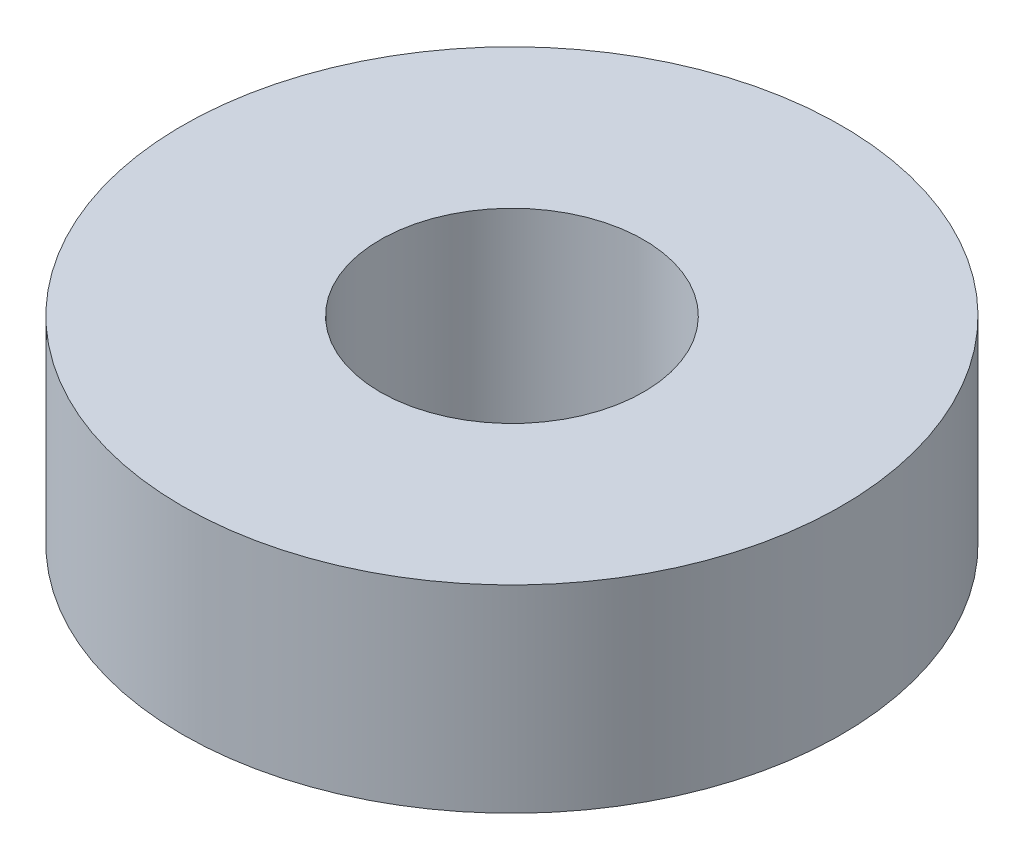
SolidWorks part; units mm, degrees
ref_plane "Front Plane" through (0, 0, 0) normal (0, 0, 1) x (1, 0, 0)
ref_plane "Top Plane" through (0, 0, 0) normal (0, 1, 0) x (1, 0, 0)
ref_plane "Right Plane" through (0, 0, 0) normal (1, 0, 0) x (0, 0, -1)
sketch "Sketch1" plane through (0, 0, 0) normal (0, 1, 0) x (1, 0, 0)
  circle A0 centre (0, 0) radius 7.9375
  dimension "D1" = 15.875
extrude "Boss-Extrude1" add sketch "Sketch1" along normal blind 4.7625
sketch "Sketch2" plane through (0, 4.7625, 0) normal (0, 1, 0) x (1, 0, 0)
  circle A0 centre (0, 0) radius 3.175
  dimension "D1" = 6.35
extrude "Cut-Extrude1" cut sketch "Sketch2" against normal through all
